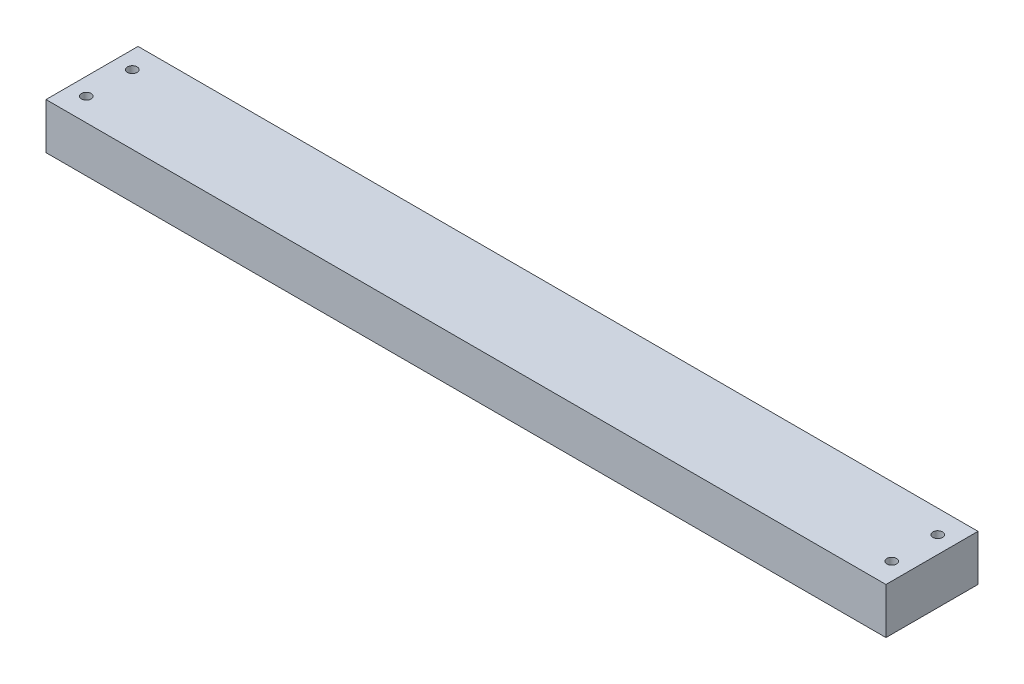
SolidWorks part; units mm, degrees
ref_plane "Front Plane" through (0, 0, 0) normal (0, 0, 1) x (1, 0, 0)
ref_plane "Top Plane" through (0, 0, 0) normal (0, 1, 0) x (1, 0, 0)
ref_plane "Right Plane" through (0, 0, 0) normal (1, 0, 0) x (0, 0, -1)
sketch "Sketch1" plane through (0, 0, 0) normal (1, 0, 0) x (0, 0, -1)
  line L1 (-25.4, -12.7) -> (25.4, -12.7)
  line L2 (-25.4, -12.7) -> (-25.4, 12.7)
  line L3 (-25.4, 12.7) -> (25.4, 12.7)
  line L4 (25.4, -12.7) -> (25.4, 12.7)
  line L5 (-25.4, -12.7) -> (25.4, 12.7) construction
  line L6 (-25.4, 12.7) -> (25.4, -12.7) construction
  point P0 (0, 0)
  dimension "D1" = 50.8
  dimension "D2" = 25.4
extrude "Boss-Extrude1" add sketch "Sketch1" along normal blind 463.55 contours L3 L4 L1 L2
sketch "Sketch2" plane through (0, 12.7, 0) normal (0, 1, 0) x (1, 0, 0)
  line L0 (463.55, 25.4) -> (0, 25.4) construction
  line L1 (231.775, 25.4) -> (231.775, -25.4) construction
  line L2 (463.55, -25.4) -> (0, -25.4) construction
  circle A0 centre (9.525, 12.7) radius 2.667
  circle A1 centre (9.525, -12.7) radius 2.667
  circle A2 centre (454.025, -12.7) radius 2.667
  circle A3 centre (454.025, 12.7) radius 2.667
  dimension "D1" = 5.334
  dimension "D2" = 5.334
  dimension "D3" = 5.334
  dimension "D4" = 5.334
  dimension "D5" = 25.4
  dimension "D6" = 12.7
  dimension "D7" = 12.7
  dimension "D8" = 25.4
  dimension "D9" = 222.25
  dimension "D10" = 222.25
  dimension "D11" = 222.25
  dimension "D12" = 222.25
extrude "Cut-Extrude1" cut sketch "Sketch2" against normal up to next
equation "\"D9@Sketch2\"=17.5/2"
